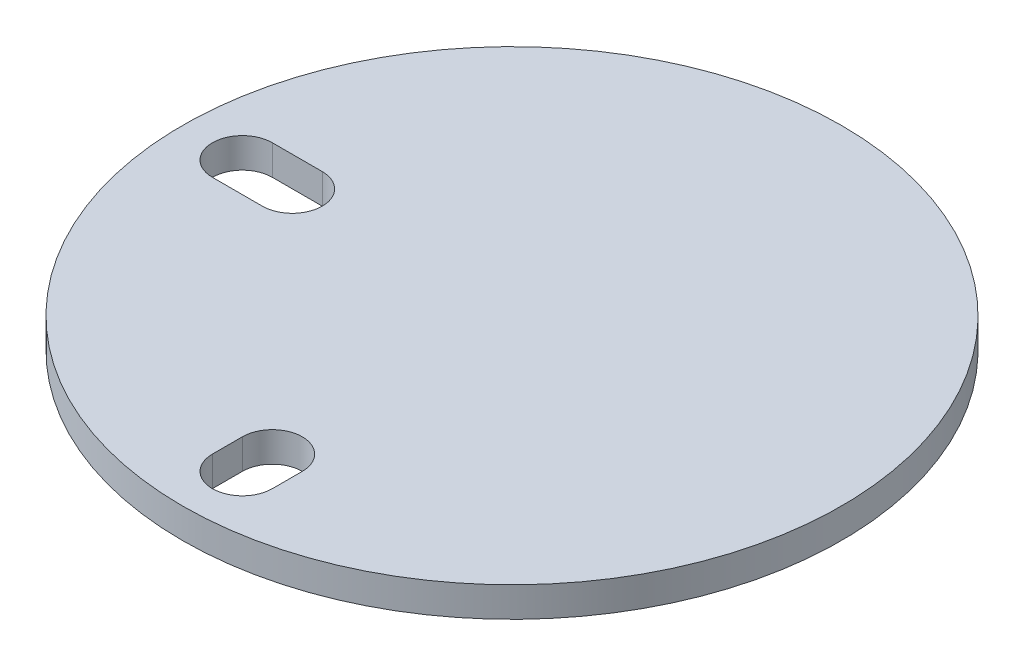
SolidWorks part; units mm, degrees
ref_plane "Ebene vorne" through (0, 0, 0) normal (0, 0, 1) x (1, 0, 0)
ref_plane "Ebene oben" through (0, 0, 0) normal (0, 1, 0) x (1, 0, 0)
ref_plane "Ebene rechts" through (0, 0, 0) normal (1, 0, 0) x (0, 0, -1)
sketch "Sketch1" plane through (0, 0, 0) normal (0, 1, 0) x (1, 0, 0)
  line L0 (0, 34.9236) -> (0, -24) construction
  line L1 (-42.4293, 0) -> (60.4566, 0) construction
  line L2 (-27, 3) -> (-22, 3)
  line L3 (-27, -3) -> (-21.9636, -2.9998)
  line L4 (-3, -27) -> (-3, -24)
  line L5 (3, -24) -> (3, -27)
  line L6 (0, -27) -> (0, -37.6654) construction
  circle A0 centre (0, 0) radius 33
  arc A1 (-21.9636, -2.9998) -> (-22, 3) centre (-22, 0) ccw
  arc A2 (3, -24) -> (-3, -24) centre (0, -24) ccw
  arc A3 (-27, 3) -> (-27, -3) centre (-27, 0) ccw
  arc A5 (-3, -27) -> (3, -27) centre (0, -27) ccw
  point P10 (-23.9636, 0)
  dimension "D1" = 66
  dimension "D2" = 6
  dimension "D3" = 6
  dimension "D6" = 6
  dimension "D4" = 22
  dimension "D5" = 24
  dimension "D7" = 5
extrude "Boss-Extrude1" add sketch "Sketch1" along normal blind 3
